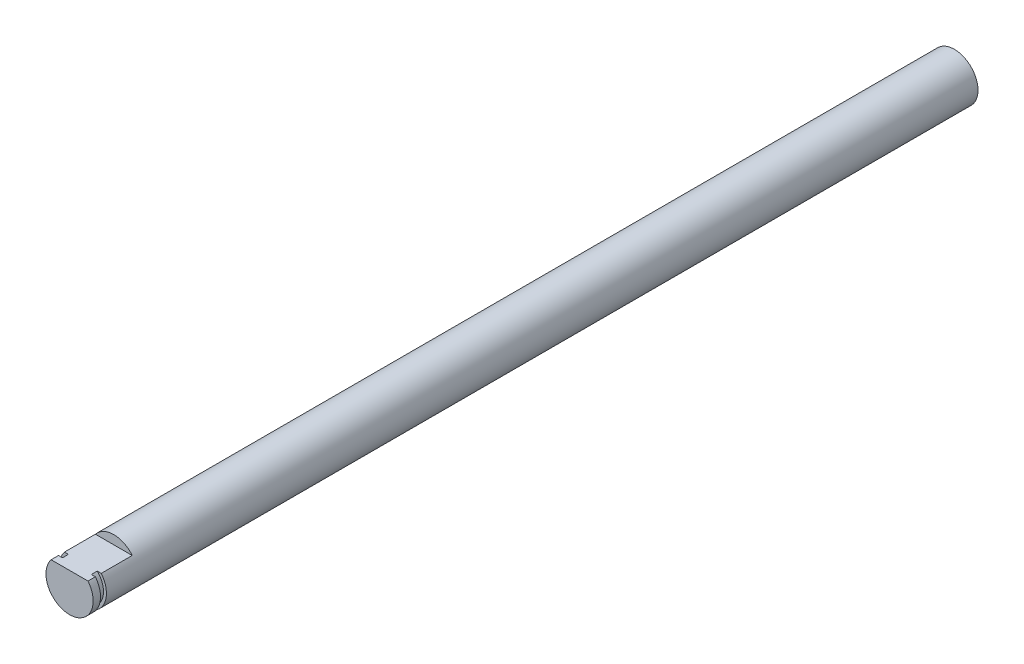
SolidWorks part; units mm, degrees
ref_plane "Front Plane" through (0, 0, 0) normal (0, 0, 1) x (1, 0, 0)
ref_plane "Top Plane" through (0, 0, 0) normal (0, 1, 0) x (1, 0, 0)
ref_plane "Right Plane" through (0, 0, 0) normal (1, 0, 0) x (0, 0, -1)
sketch "Sketch1" plane through (0, 0, 0) normal (0, 0, 1) x (1, 0, 0)
  circle A0 centre (0, 0) radius 4
  dimension "D1" = 8
extrude "Boss-Extrude1" add sketch "Sketch1" along normal blind 150
sketch "Sketch2" plane through (0, 0, 150) normal (0, 0, 1) x (1, 0, 0)
  line L0 (3.1225, 2.5) -> (-3.1225, 2.5)
  circle A1 centre (0, 0) radius 4
  arc A2 (3.1225, 2.5) -> (-3.1225, 2.5) centre (0, 0) ccw
  dimension "D2" = 2.5
  dimension "D1" = 0
extrude "Cut-Extrude1" cut sketch "Sketch2" against normal blind 7.5
ref_plane "Plane1" through (0, 0, 148.75) normal (0, 0, 1) x (1, 0, 0)
sketch "Sketch3" plane through (0, 0, 148.75) normal (0, 0, 1) x (1, 0, 0)
  circle A0 centre (0, 0) radius 4
  circle A1 centre (0, 0) radius 3.5
extrude "Cut-Extrude2" cut sketch "Sketch3" against normal blind 1
